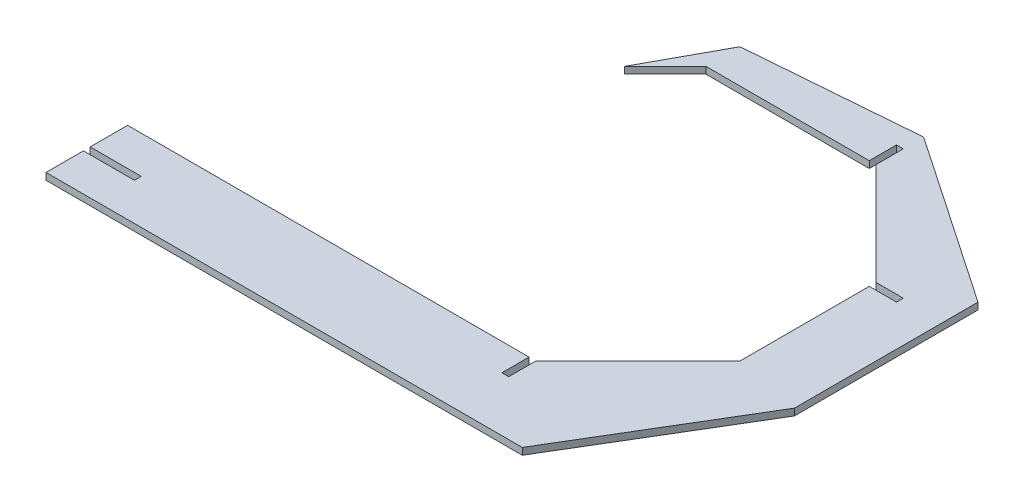
SolidWorks part; units mm, degrees
ref_plane "Front Plane" through (0, 0, 0) normal (0, 0, 1) x (1, 0, 0)
ref_plane "Top Plane" through (0, 0, 0) normal (0, 1, 0) x (1, 0, 0)
ref_plane "Right Plane" through (0, 0, 0) normal (1, 0, 0) x (0, 0, -1)
sketch "Sketch1" plane through (0, 0, 0) normal (0, 1, 0) x (1, 0, 0)
  line L0 (0, 0) -> (0, -30.48)
  line L1 (0, -30.48) -> (177.8, -30.48)
  line L2 (152.4, 0) -> (190.5, 38.1)
  line L3 (0, 0) -> (152.4, 0)
  line L4 (190.5, 38.1) -> (190.5, 88.9)
  line L5 (190.5, 88.9) -> (152.4, 127)
  line L6 (152.4, 127) -> (88.9, 127)
  line L7 (88.9, 127) -> (73.66, 111.76)
  line L8 (73.66, 111.76) -> (88.9, 139.7)
  line L9 (88.9, 139.7) -> (152.4, 144.78)
  line L10 (152.4, 144.78) -> (215.9, 101.5553)
  line L11 (215.9, 101.5553) -> (215.9, 33.02)
  line L12 (215.9, 33.02) -> (177.8, -30.48)
  dimension "D1" = 30.48
  dimension "D2" = 152.4
  dimension "D3" = 177.8
  dimension "D4" = 38.1
  dimension "D5" = 63.5
  dimension "D6" = 25.4
  dimension "D7" = 38.1
  dimension "D8" = 68.5353
  dimension "D9" = 50.8
  dimension "D10" = 38.1
  dimension "D11" = 17.78
  dimension "D12" = 12.7
  dimension "D13" = 15.24
  dimension "D14" = 0
  dimension "D15" = 27.94
  dimension "D16" = 63.5
extrude "Boss-Extrude1" add sketch "Sketch1" along normal blind 2.54
sketch "Sketch2" plane through (0, 2.54, 0) normal (0, 1, 0) x (1, 0, 0)
  line L0 (0, 0) -> (0, -30.48) construction
  line L1 (0, -13.97) -> (19.05, -13.97)
  line L2 (0, -13.97) -> (0, -16.51)
  line L3 (0, -16.51) -> (19.05, -16.51)
  line L4 (19.05, -13.97) -> (19.05, -16.51)
  line L5 (152.4, 0) -> (0, 0) construction
  line L7 (152.4, 0) -> (149.86, 0)
  line L8 (152.4, 0) -> (152.4, -10.16)
  line L9 (152.4, -10.16) -> (149.86, -10.16)
  line L10 (149.86, 0) -> (149.86, -10.16)
  line L11 (190.5, 88.9) -> (200.66, 88.9)
  line L12 (190.5, 88.9) -> (190.5, 86.36)
  line L13 (190.5, 86.36) -> (200.66, 86.36)
  line L14 (200.66, 88.9) -> (200.66, 86.36)
  line L15 (152.4, 127) -> (149.86, 127)
  line L16 (152.4, 127) -> (152.4, 137.16)
  line L17 (152.4, 137.16) -> (149.86, 137.16)
  line L18 (149.86, 127) -> (149.86, 137.16)
  dimension "D1" = 19.05
  dimension "D2" = 2.54
  dimension "D3" = 13.97
  dimension "D4" = 2.54
  dimension "D5" = 10.16
  dimension "D6" = 10.16
  dimension "D7" = 2.54
  dimension "D8" = 10.16
  dimension "D9" = 2.54
extrude "Cut-Extrude1" cut sketch "Sketch2" against normal through all
